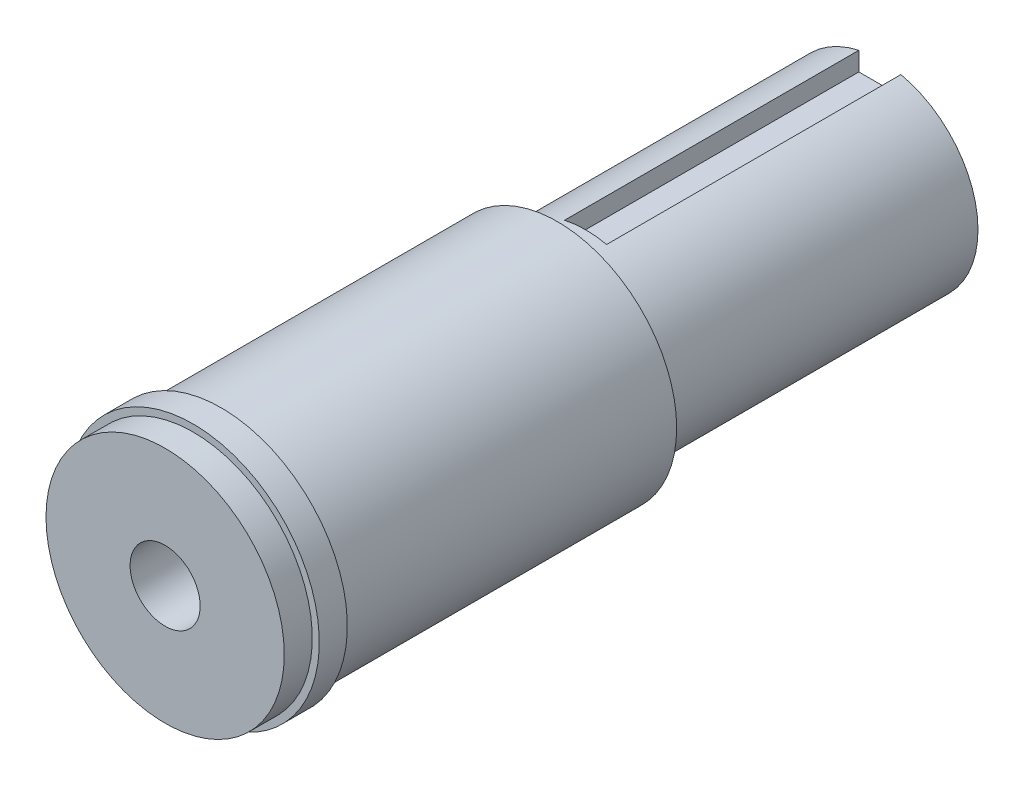
SolidWorks part; units mm, degrees
material "Plain Carbon Steel"
ref_plane "Front Plane" through (0, 0, 0) normal (0, 0, 1) x (1, 0, 0)
ref_plane "Top Plane" through (0, 0, 0) normal (0, 1, 0) x (1, 0, 0)
ref_plane "Right Plane" through (0, 0, 0) normal (1, 0, 0) x (0, 0, -1)
sketch "Sketch1" plane through (0, 0, 0) normal (0, 0, 1) x (1, 0, 0)
  circle A0 centre (0, 0) radius 7
  dimension "D1" = 14
extrude "Boss-Extrude1" add sketch "Sketch1" along normal blind 23
sketch "Sketch3" plane through (0, 0, 0) normal (0, 0, -1) x (-1, 0, 0)
  line L0 (0, 55) -> (0, -55) construction
  line L1 (-1.5, 5.5) -> (1.5, 5.5)
  line L2 (-1.5, 5.5) -> (-1.5, 8.5)
  line L3 (-1.5, 8.5) -> (1.5, 8.5)
  line L4 (1.5, 5.5) -> (1.5, 8.5)
  line L5 (-1.5, 5.5) -> (1.5, 8.5) construction
  line L6 (-1.5, 8.5) -> (1.5, 5.5) construction
  circle A0 centre (0, 0) radius 7 construction
  point P0 (0, 7)
  dimension "D1" = 1.5
  dimension "D2" = 3
extrude "Cut-Extrude1" cut sketch "Sketch3" against normal blind 21
sketch "Sketch6" plane through (0, 0, 23) normal (0, 0, 1) x (1, 0, 0)
  circle A0 centre (0, 0) radius 8.5
  dimension "D1" = 17
extrude "Boss-Extrude2" add sketch "Sketch6" along normal blind 28
ref_plane "Plane2" through (0, 0, 47) normal (0, 0, -1) x (-1, 0, 0)
sketch "Sketch7" plane through (0, 0, 47) normal (0, 0, -1) x (-1, 0, 0)
  circle A0 centre (0, 0) radius 9
  dimension "D1" = 18
extrude "Boss-Extrude3" add sketch "Sketch7" against normal blind 2
hole_wizard "M6x1.0 Tapped Hole1" positions "Sketch9" profile "Sketch10" tap size "M6x1.0" standard "ANSI Metric"
sketch "Sketch9" plane through (0, 0, 51) normal (0, 0, 1) x (1, 0, 0)
  point P0 (0, 0)
sketch "Sketch10" plane through (0, 0, 51) normal (1, 0, 0) x (0, -1, 0)
  line L0 (0, 0) -> (0, 21.5022)
  line L1 (0, 21.5022) -> (2.5, 20)
  line L2 (2.5, 20) -> (2.5, 0)
  line L5 (2.5, 0) -> (0, 0)
  line L10 (0, 21.5022) -> (-2.5, 20) construction
  line L11 (0, -6.35) -> (0, 107.95) construction
  dimension "Tap Drill Dia." = 5
  dimension "Tap Drill Depth" = 20
  dimension "Drill Angle" = 118
